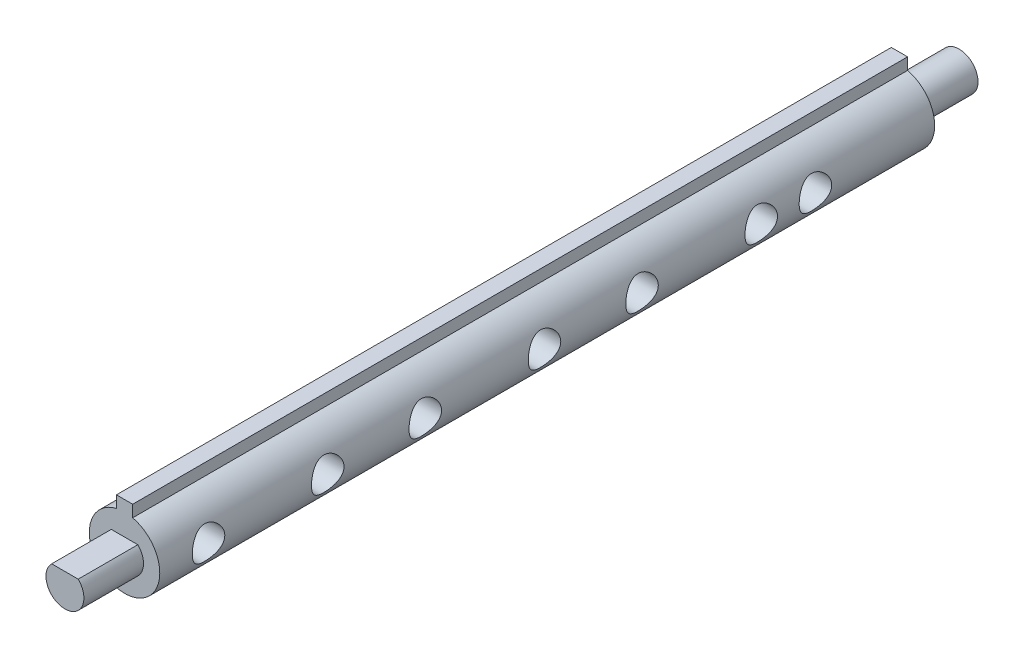
SolidWorks part; units mm, degrees
ref_plane "前视基准面" through (0, 0, 0) normal (0, 0, 1) x (1, 0, 0)
ref_plane "上视基准面" through (0, 0, 0) normal (0, 1, 0) x (1, 0, 0)
ref_plane "右视基准面" through (0, 0, 0) normal (1, 0, 0) x (0, 0, -1)
sketch "草图1" plane through (0, 0, 0) normal (0, 0, 1) x (1, 0, 0)
  line L0 (1.5, 4.5) -> (1.5, 6.3246) construction
  line L1 (-1.5, 4.5) -> (1.5, 4.5) construction
  line L2 (-1.5, 6.3246) -> (-1.5, 8.5)
  line L3 (-1.5, 8.5) -> (1.5, 8.5)
  line L4 (1.5, 6.3246) -> (1.5, 8.5)
  line L5 (0, 6.5) -> (1.5, 8.5) construction
  line L6 (-1.5, 8.5) -> (0, 6.5) construction
  line L7 (0, 6.5) -> (1.5, 4.5) construction
  line L8 (-1.5, 4.5) -> (0, 6.5) construction
  line L9 (-1.5, 4.5) -> (-1.5, 6.3246) construction
  arc A0 (-1.5, 6.3246) -> (1.5, 6.3246) centre (0, 0) ccw
  arc A1 (0, 6.5) -> (-1.5, 6.3246) centre (0, 0) ccw construction
  arc A2 (1.5, 6.3246) -> (0, 6.5) centre (0, 0) ccw construction
  point P3 (0, 6.5)
  dimension "D1" = 13
  dimension "D2" = 2
  dimension "D3" = 3
extrude "凸台-拉伸1" add sketch "草图1" along normal blind 143
sketch "草图2" plane through (0, 0, 143) normal (0, 0, 1) x (1, 0, 0)
  circle A0 centre (0, 0) radius 3.5
  dimension "D1" = 7
extrude "凸台-拉伸2" add sketch "草图2" along normal blind 11
sketch "草图3" plane through (0, 0, 0) normal (0, 0, -1) x (-1, 0, 0)
  circle A0 centre (0, 0) radius 3.5
  dimension "D1" = 7
extrude "凸台-拉伸3" add sketch "草图3" along normal blind 11
sketch "草图4" plane through (0, 0, -11) normal (0, 0, -1) x (-1, 0, 0)
  line L1 (-9.9341, 0) -> (-3.5, 0) construction
  line L2 (-2.4495, -2.5) -> (2.4495, -2.5)
  line L3 (3.5, 0) -> (14.3106, 0) construction
  arc A3 (-2.4495, -2.5) -> (2.4495, -2.5) centre (0, 0) ccw construction
  arc A4 (2.4495, -2.5) -> (-2.4495, -2.5) centre (0, 0) cw
extrude "切除-拉伸1" cut sketch "草图4" against normal blind 11
sketch "草图5" plane through (0, 0, 154) normal (0, 0, 1) x (1, 0, 0)
  line L0 (-2.4495, 2.5) -> (2.4495, 2.5)
  arc A0 (2.4495, 2.5) -> (-2.4495, 2.5) centre (0, 0) ccw
  arc A1 (-2.4495, 2.5) -> (2.4495, 2.5) centre (0, 0) ccw construction
  dimension "D2" = 7
  dimension "D1" = 2.5
extrude "切除-拉伸2" cut sketch "草图5" against normal blind 11
sketch "草图7" plane through (0, 0, 0) normal (1, 0, 0) x (0, 0, -1)
  line L0 (-143, -6.5) -> (0, -6.5) construction
  line L2 (0, -2.5) -> (0, 3.5) construction
  line L3 (0, -6.5) -> (0, 6.3246) construction
  circle A0 centre (-134, 0) radius 3
  circle A1 centre (-112, 0) radius 3
  circle A2 centre (-94, 0) radius 3
  circle A3 centre (-72, 0) radius 3
  circle A4 centre (-54, 0) radius 3
  circle A5 centre (-32, 0) radius 3
  circle A6 centre (-22, 0) radius 3
  dimension "D2" = 6
  dimension "D3" = 6
  dimension "D7" = 6
  dimension "D8" = 6
  dimension "D10" = 6
  dimension "D11" = 6
  dimension "D15" = 6
  dimension "D1" = 22
  dimension "D4" = 6.5
  dimension "D5" = 6.5
  dimension "D6" = 22
  dimension "D9" = 22
  dimension "D12" = 18
  dimension "D13" = 18
  dimension "D14" = 32
  dimension "D16" = 22
extrude "切除-拉伸3" cut sketch "草图7" along normal mid plane 20
